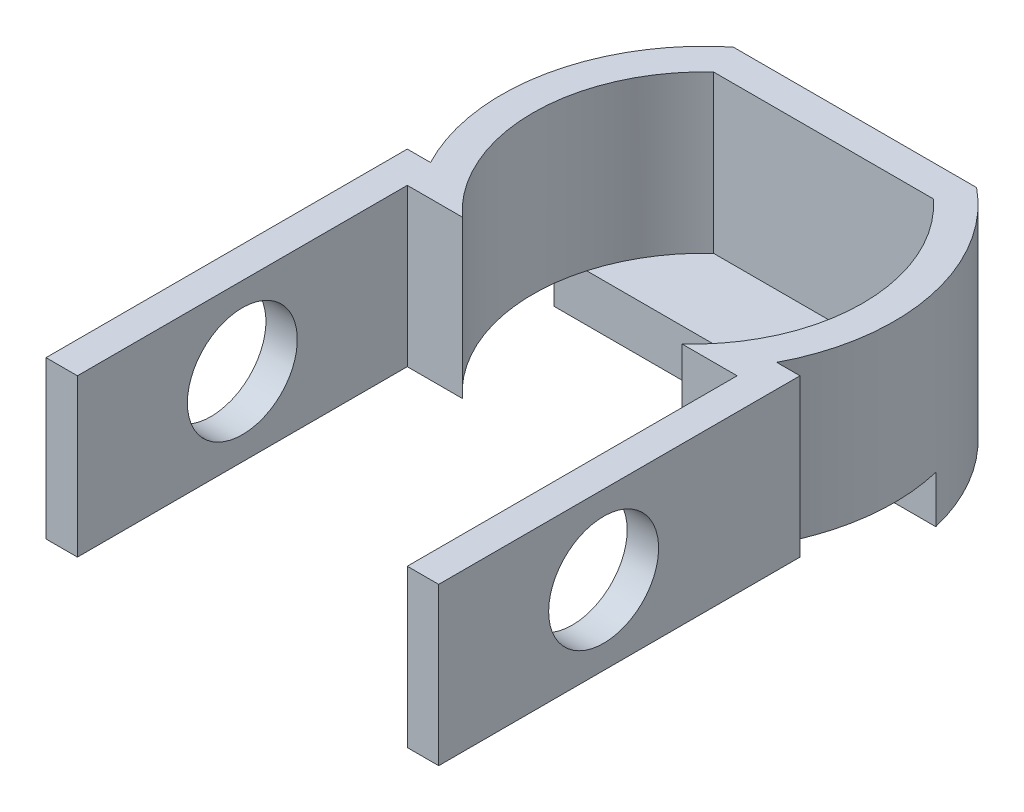
SolidWorks part; units mm, degrees
ref_plane "Front Plane" through (0, 0, 0) normal (0, 0, 1) x (1, 0, 0)
ref_plane "Top Plane" through (0, 0, 0) normal (0, 1, 0) x (1, 0, 0)
ref_plane "Right Plane" through (0, 0, 0) normal (1, 0, 0) x (0, 0, -1)
sketch "Sketch1" plane through (0, 0, 0) normal (0, 1, 0) x (1, 0, 0)
  line L1 (7, 16) -> (-7, 16)
  line L2 (-10.5, 22.4884) -> (-10.5, -1.9608) construction
  line L3 (10.5, 30.5265) -> (10.5, -9.8649) construction
  line L4 (7, 0) -> (10.5, 0)
  line L5 (-10.5, 0) -> (-7, 0)
  line L6 (-10.5, 0) -> (-10.5, -21)
  line L8 (10.5, 0) -> (10.5, -21)
  line L9 (0.3929, 8) -> (7, 16) construction
  line L10 (-0.3929, 8) -> (-7, 16) construction
  line L11 (12.5, 2) -> (12.5, -21)
  line L12 (11.0188, 2) -> (12.5, 2)
  line L13 (7.7451, 18) -> (-7.7451, 18)
  line L14 (-12.5, 2) -> (-11.0188, 2)
  line L15 (-12.5, 2) -> (-12.5, -21)
  line L16 (-12.5, -21) -> (-10.5, -21)
  line L17 (10.5, -21) -> (12.5, -21)
  arc A2 (7, 16) -> (7, 0) centre (-0.3929, 8) cw
  arc A3 (-7, 16) -> (-7, 0) centre (0.3929, 8) ccw
  arc A4 (7.7451, 18) -> (11.0188, 2) centre (-0.3929, 8) cw
  arc A5 (-7.7451, 18) -> (-11.0188, 2) centre (0.3929, 8) ccw
  point P3 (0, 16)
  dimension "D1" = 14
  dimension "D3" = 21
  dimension "D4" = 21
  dimension "D2" = 10.8929
  dimension "D5" = 3.5
  dimension "D6" = 21
  dimension "D7" = 2
extrude "Boss-Extrude1" add sketch "Sketch1" along normal blind 10
sketch "Sketch2" plane through (-12.5, 0, 0) normal (-1, 0, 0) x (0, 0, 1)
  line L0 (21, 10) -> (21, 0) construction
  circle A0 centre (10.5, 5) radius 3.5
  point P4 (21, 5)
  dimension "D1" = 7
  dimension "D2" = 10.5
extrude "Cut-Extrude1" cut sketch "Sketch2" against normal through all
sketch "Sketch3" plane through (0, 0, 0) normal (0, -1, 0) x (1, 0, 0)
  line L0 (-12.1461, -11) -> (12.1461, -11)
  line L2 (7.7451, -18) -> (-7.7451, -18)
  arc A0 (-11.0188, -2) -> (-7.7451, -18) centre (0.3929, -8) ccw construction
  arc A1 (7.7451, -18) -> (11.0188, -2) centre (-0.3929, -8) ccw construction
  arc A3 (-12.1461, -11) -> (-7.7451, -18) centre (0.3929, -8) ccw
  arc A4 (7.7451, -18) -> (12.1461, -11) centre (-0.3929, -8) ccw
  dimension "D1" = 7
extrude "Boss-Extrude2" add sketch "Sketch3" along normal blind 3
